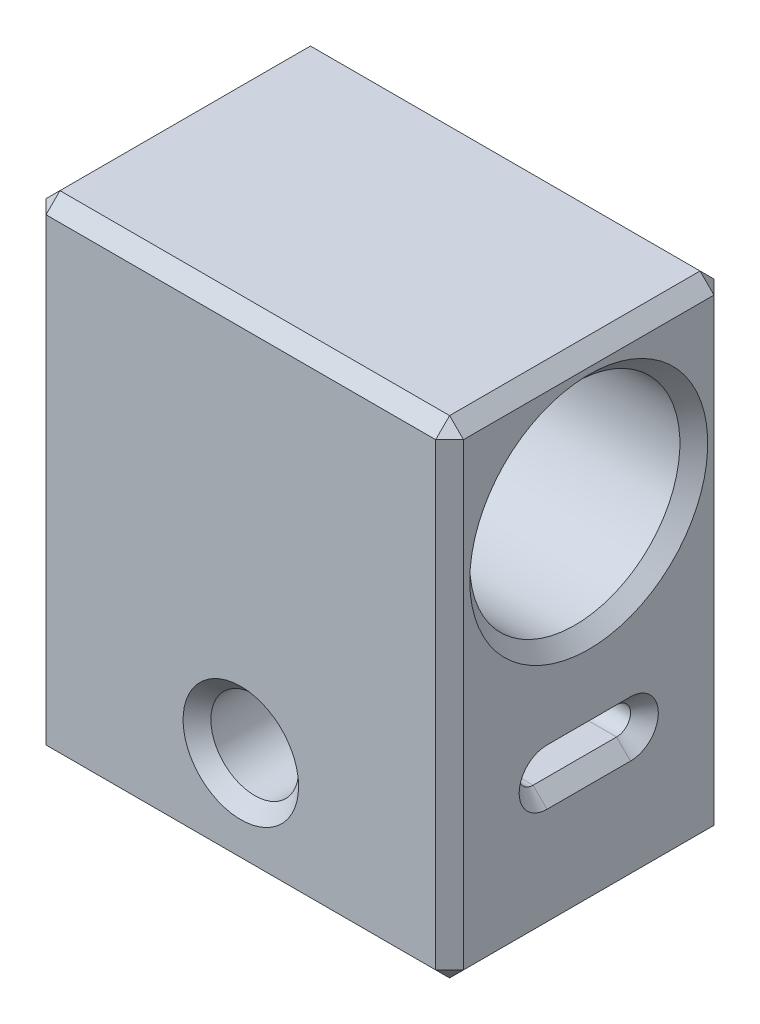
SolidWorks part; units mm, degrees
ref_plane "前视基准面" through (0, 0, 0) normal (0, 0, 1) x (1, 0, 0)
ref_plane "上视基准面" through (0, 0, 0) normal (0, 1, 0) x (1, 0, 0)
ref_plane "右视基准面" through (0, 0, 0) normal (1, 0, 0) x (0, 0, -1)
other "Configuration Table"
sketch "草图1" plane through (0, 0, 0) normal (1, 0, 0) x (0, 0, -1)
  line L0 (0, 0) -> (0, 35)
  line L1 (0, 35) -> (20, 35)
  line L2 (20, 35) -> (20, 0)
  line L3 (20, 0) -> (0, 0)
  line L4 (10, 35) -> (10, 0) construction
  circle A0 centre (10, 25) radius 7.55
  dimension "D3" = 15.1
  dimension "D1" = 35
  dimension "D2" = 20
  dimension "D4" = 10
extrude "凸台-拉伸1" add sketch "草图1" along normal blind 30
sketch "草图2" plane through (0, 0, 0) normal (0, 0, 1) x (1, 0, 0)
  line L0 (0, 25) -> (30, 25) construction
  line L1 (0, 35) -> (0, 0) construction
  line L2 (30, 35) -> (30, 0) construction
  line L3 (30, 35) -> (0, 35) construction
  line L4 (0, 7.5) -> (30, 7.5) construction
  circle A0 centre (15, 7.5) radius 3.15
  dimension "D3" = 6.3
  dimension "D1" = 10
  dimension "D2" = 17.5
extrude "切除-拉伸1" cut sketch "草图2" against normal up to next
sketch "草图3" plane through (30, 0, 0) normal (1, 0, 0) x (0, 0, -1)
  line L0 (10, 25) -> (10, 10) construction
  line L1 (7, 10) -> (13, 10) construction
  line L2 (7, 11) -> (13, 11)
  line L3 (7, 9) -> (13, 9)
  arc A0 (7, 11) -> (7, 9) centre (7, 10) ccw
  arc A1 (13, 9) -> (13, 11) centre (13, 10) ccw
  point P5 (10, 10)
  dimension "D1" = 15
  dimension "D2" = 6
  dimension "D3" = 2
extrude "切除-拉伸2" cut sketch "草图3" against normal blind 10
sketch "草图4" plane through (0, 0, 0) normal (-1, 0, 0) x (0, 0, 1)
  line L0 (-7, 9) -> (-13, 9) construction
  line L1 (-13, 11) -> (-7, 11) construction
  line L2 (-7, 9) -> (-13, 9)
  line L3 (-13, 11) -> (-7, 11)
  arc A0 (-13, 11) -> (-13, 9) centre (-13, 10) ccw construction
  arc A1 (-7, 9) -> (-7, 11) centre (-7, 10) ccw construction
  arc A2 (-13, 11) -> (-13, 9) centre (-13, 10) ccw
  arc A3 (-7, 9) -> (-7, 11) centre (-7, 10) ccw
extrude "切除-拉伸3" cut sketch "草图4" against normal blind 10
sketch "草图5" plane through (0, 0, 0) normal (0, -1, 0) x (1, 0, 0)
  line L0 (0, -10) -> (30, -10) construction
  line L1 (0, 0) -> (0, -20) construction
  line L2 (30, 0) -> (30, -20) construction
  line L3 (15, 0) -> (15, -20) construction
  line L4 (30, 0) -> (0, 0) construction
  line L5 (30, -20) -> (0, -20) construction
  circle A0 centre (5, -10) radius 1.4
  circle A1 centre (25, -10) radius 1.4
  dimension "D1" = 2.8
  dimension "D2" = 5
extrude "切除-拉伸4" cut sketch "草图5" against normal blind 13
chamfer "倒角1" distance 1 angle 45 24 edges at (15, 4.35, -20) (30, 25, -17.55) (30, 10, -14) (30, 11, -10) (30, 10, -6) (30, 9, -10) (18.15, 7.5, 0) (0, 25, -17.55) (15, 0, -20) (15, 35, -20) (30, 35, -10) (30, 17.5, -20) (30, 0, -10) (15, 35, 0) (30, 17.5, 0) (15, 0, 0) (0, 17.5, -20) (0, 35, -10) (0, 17.5, 0) (0, 0, -10) (0, 11, -10) (0, 10, -14) (0, 9, -10) (0, 10, -6)
chamfer "倒角2" distance 1.5 angle 45 2 edges at (25, 0, -8.6) (5, 0, -11.4)
